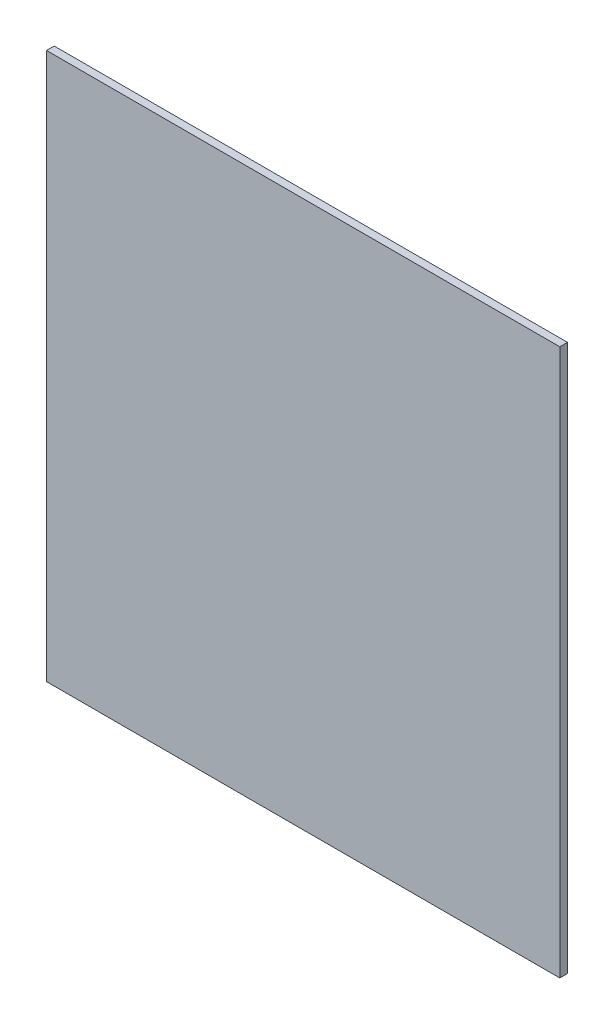
SolidWorks part; units mm, degrees
ref_plane "Front" through (0, 0, 0) normal (0, 0, 1) x (1, 0, 0)
ref_plane "Top" through (0, 0, 0) normal (0, 1, 0) x (1, 0, 0)
ref_plane "Right" through (0, 0, 0) normal (1, 0, 0) x (0, 0, -1)
sketch "Sketch1" plane through (0, 0, 0) normal (0, 0, 1) x (1, 0, 0)
  line L1 (-100, -106.5) -> (100, -106.5)
  line L2 (-100, -106.5) -> (-100, 106.5)
  line L3 (-100, 106.5) -> (100, 106.5)
  line L4 (100, -106.5) -> (100, 106.5)
  point P4 (-100, 0)
  point P5 (0, 106.5)
  dimension "D1" = 200
  dimension "D2" = 213
extrude "Boss-Extrude1" add sketch "Sketch1" along normal blind 3
